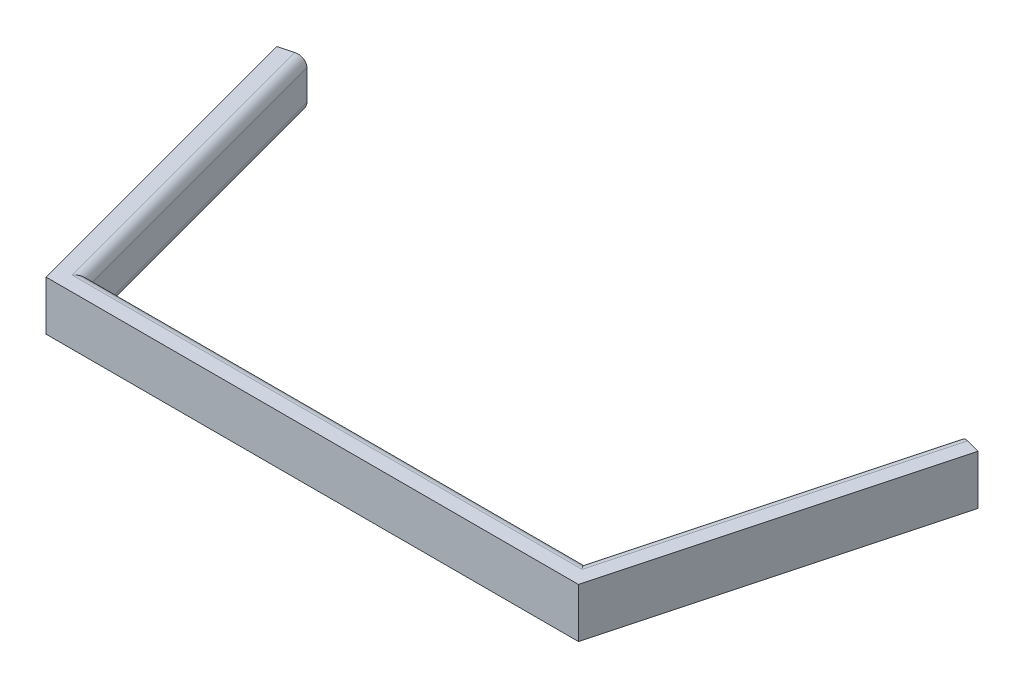
SolidWorks part; units mm, degrees
ref_plane "Front Plane" through (0, 0, 0) normal (0, 0, 1) x (1, 0, 0)
ref_plane "Top Plane" through (0, 0, 0) normal (0, 1, 0) x (1, 0, 0)
ref_plane "Right Plane" through (0, 0, 0) normal (1, 0, 0) x (0, 0, -1)
sketch "Sketch1" plane through (0, 0, 0) normal (0, 1, 0) x (1, 0, 0)
  line L0 (0, 0) -> (0, 99.1868) construction
  line L1 (-83.9177, 76.2) -> (-63.5, 0)
  line L2 (-63.5, 0) -> (63.5, 0)
  line L3 (0, 0) -> (0, -6.35)
  line L4 (68.3725, -6.35) -> (-68.3725, -6.35)
  line L5 (-68.3725, -6.35) -> (-90.0514, 74.5565)
  line L6 (-90.0514, 74.5565) -> (-83.9177, 76.2)
  line L7 (90.0514, 74.5565) -> (83.9177, 76.2)
  line L8 (68.3725, -6.35) -> (90.0514, 74.5565)
  line L9 (83.9177, 76.2) -> (63.5, 0)
  dimension "D1" = 127
  dimension "D2" = 105
  dimension "D3" = 76.2
  dimension "D4" = 6.35
  dimension "D5" = 6.35
extrude "Extrude1" add sketch "Sketch1" along normal blind 12.7 contours L6 L5 L4 L3 L2 L1 | L7 L9 L2 L3 L4 L8
fillet "Fillet1" radius 2.54 6 edges at (-73.7089, 0, -38.1) (0, 0, 0) (73.7089, 0, -38.1) (73.7089, 12.7, -38.1) (0, 12.7, 0) (-73.7089, 12.7, -38.1)
